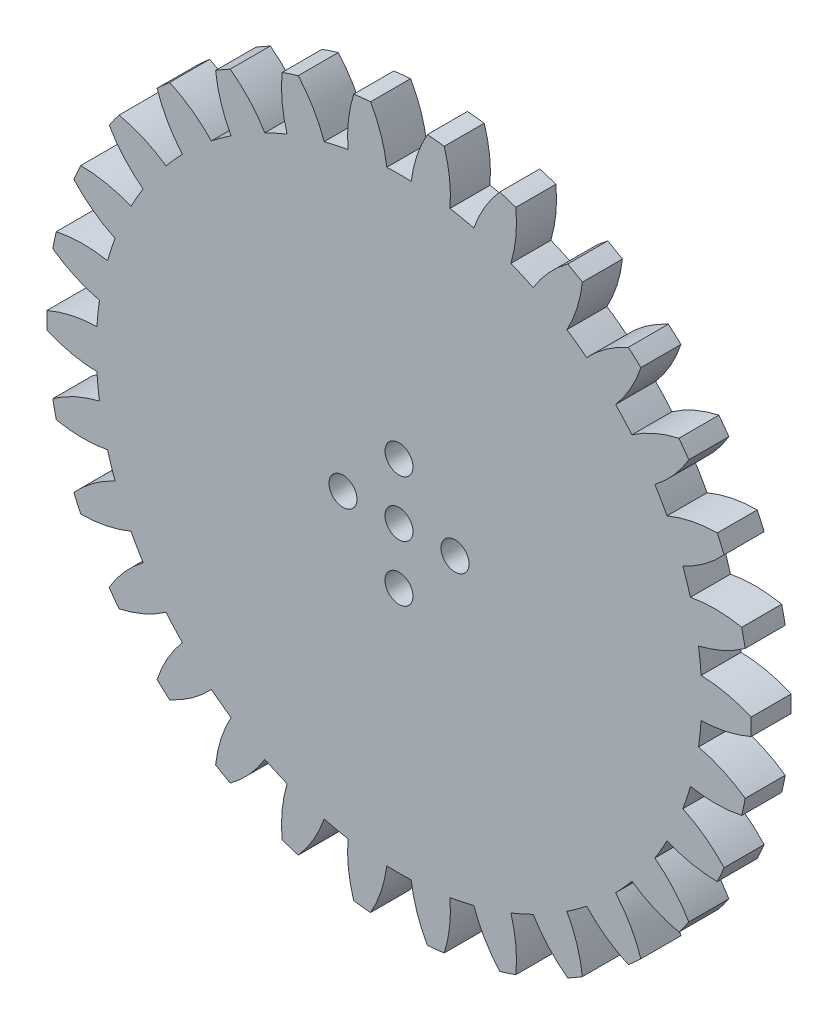
SolidWorks part; units mm, degrees
ref_plane "前视基准面" through (0, 0, 0) normal (0, 0, 1) x (1, 0, 0)
ref_plane "上视基准面" through (0, 0, 0) normal (0, 1, 0) x (1, 0, 0)
ref_plane "右视基准面" through (0, 0, 0) normal (1, 0, 0) x (0, 0, -1)
sketch "草图1" plane through (0, 0, 0) normal (0, 0, 1) x (1, 0, 0)
  arc A0 (-43.9873, -1.0569) -> (-37.7331, -2.4344) centre (-37.3786, 14.0618) ccw
  arc A1 (-37.7331, -2.4344) -> (-37.4146, -5.4639) centre (0, 0) ccw
  arc A2 (-37.4146, -5.4639) -> (-43.2458, -8.1117) centre (-33.6381, -21.5259) ccw
  arc A3 (-43.2458, -8.1117) -> (-42.8063, -10.1793) centre (0, 0) ccw
  arc A4 (-42.8063, -10.1793) -> (-36.4024, -10.2263) centre (-39.4854, 5.9831) ccw
  arc A5 (-36.4024, -10.2263) -> (-35.461, -13.1235) centre (0, 0) ccw
  arc A6 (-35.461, -13.1235) -> (-40.6143, -16.9257) centre (-28.4276, -28.0493) ccw
  arc A7 (-40.6143, -16.9257) -> (-39.7545, -18.8568) centre (0, 0) ccw
  arc A8 (-39.7545, -18.8568) -> (-33.4807, -17.5714) centre (-39.8665, -2.3572) ccw
  arc A9 (-33.4807, -17.5714) -> (-31.9576, -20.2095) centre (0, 0) ccw
  arc A10 (-31.9576, -20.2095) -> (-36.2077, -25) centre (-21.9746, -33.3468) ccw
  arc A11 (-36.2077, -25) -> (-34.9652, -26.7101) centre (0, 0) ccw
  arc A12 (-34.9652, -26.7101) -> (-29.0958, -24.1484) centre (-38.5052, -10.5943) ccw
  arc A13 (-29.0958, -24.1484) -> (-27.0575, -26.4122) centre (0, 0) ccw
  arc A14 (-27.0575, -26.4122) -> (-30.2187, -31.9817) centre (-14.5612, -37.1869) ccw
  arc A15 (-30.2187, -31.9817) -> (-28.6478, -33.3961) centre (0, 0) ccw
  arc A16 (-28.6478, -33.3961) -> (-23.4392, -29.6701) centre (-35.4611, -18.3685) ccw
  arc A17 (-23.4392, -29.6701) -> (-20.9748, -31.4606) centre (0, 0) ccw
  arc A18 (-20.9748, -31.4606) -> (-22.909, -37.5657) centre (-6.5114, -39.4017) ccw
  arc A19 (-22.909, -37.5657) -> (-21.0784, -38.6226) centre (0, 0) ccw
  arc A20 (-21.0784, -38.6226) -> (-16.7583, -33.895) centre (-30.8672, -25.3399) ccw
  arc A21 (-16.7583, -33.895) -> (-13.9754, -35.134) centre (0, 0) ccw
  arc A22 (-13.9754, -35.134) -> (-14.598, -41.5078) centre (1.8229, -39.8945) ccw
  arc A23 (-14.598, -41.5078) -> (-12.5877, -42.161) centre (0, 0) ccw
  arc A24 (-12.5877, -42.161) -> (-9.3449, -36.6385) centre (-24.9242, -31.2038) ccw
  arc A25 (-9.3449, -36.6385) -> (-6.3652, -37.2719) centre (0, 0) ccw
  arc A26 (-6.3652, -37.2719) -> (-5.649, -43.6359) centre (10.0776, -38.6437) ccw
  arc A27 (-5.649, -43.6359) -> (-3.5468, -43.8568) centre (0, 0) ccw
  arc A28 (-3.5468, -43.8568) -> (-1.5231, -37.7808) centre (-17.8919, -35.7039) ccw
  arc A29 (-1.5231, -37.7808) -> (1.5231, -37.7808) centre (0, 0) ccw
  arc A30 (1.5231, -37.7808) -> (3.5468, -43.8568) centre (17.8919, -35.7039) ccw
  arc A31 (3.5468, -43.8568) -> (5.649, -43.6359) centre (0, 0) ccw
  arc A32 (5.649, -43.6359) -> (6.3652, -37.2719) centre (-10.0776, -38.6437) ccw
  arc A33 (6.3652, -37.2719) -> (9.3449, -36.6385) centre (0, 0) ccw
  arc A34 (9.3449, -36.6385) -> (12.5877, -42.161) centre (24.9242, -31.2038) ccw
  arc A35 (12.5877, -42.161) -> (14.598, -41.5078) centre (0, 0) ccw
  arc A36 (14.598, -41.5078) -> (13.9754, -35.134) centre (-1.8229, -39.8945) ccw
  arc A37 (13.9754, -35.134) -> (16.7583, -33.895) centre (0, 0) ccw
  arc A38 (16.7583, -33.895) -> (21.0784, -38.6226) centre (30.8672, -25.3399) ccw
  arc A39 (21.0784, -38.6226) -> (22.909, -37.5657) centre (0, 0) ccw
  arc A40 (22.909, -37.5657) -> (20.9748, -31.4606) centre (6.5114, -39.4017) ccw
  arc A41 (20.9748, -31.4606) -> (23.4392, -29.6701) centre (0, 0) ccw
  arc A42 (23.4392, -29.6701) -> (28.6478, -33.3961) centre (35.4611, -18.3685) ccw
  arc A43 (28.6478, -33.3961) -> (30.2187, -31.9817) centre (0, 0) ccw
  arc A44 (30.2187, -31.9817) -> (27.0575, -26.4122) centre (14.5612, -37.1869) ccw
  arc A45 (27.0575, -26.4122) -> (29.0958, -24.1484) centre (0, 0) ccw
  arc A46 (29.0958, -24.1484) -> (34.9652, -26.7101) centre (38.5052, -10.5943) ccw
  arc A47 (34.9652, -26.7101) -> (36.2077, -25) centre (0, 0) ccw
  arc A48 (36.2077, -25) -> (31.9576, -20.2095) centre (21.9746, -33.3468) ccw
  arc A49 (31.9576, -20.2095) -> (33.4807, -17.5714) centre (0, 0) ccw
  arc A50 (33.4807, -17.5714) -> (39.7545, -18.8568) centre (39.8665, -2.3572) ccw
  arc A51 (39.7545, -18.8568) -> (40.6143, -16.9257) centre (0, 0) ccw
  arc A52 (40.6143, -16.9257) -> (35.461, -13.1235) centre (28.4276, -28.0493) ccw
  arc A53 (35.461, -13.1235) -> (36.4024, -10.2263) centre (0, 0) ccw
  arc A54 (36.4024, -10.2263) -> (42.8063, -10.1793) centre (39.4854, 5.9831) ccw
  arc A55 (42.8063, -10.1793) -> (43.2458, -8.1117) centre (0, 0) ccw
  arc A56 (43.2458, -8.1117) -> (37.4146, -5.4639) centre (33.6381, -21.5259) ccw
  arc A57 (37.4146, -5.4639) -> (37.7331, -2.4344) centre (0, 0) ccw
  arc A58 (37.7331, -2.4344) -> (43.9873, -1.0569) centre (37.3786, 14.0618) ccw
  arc A59 (43.9873, -1.0569) -> (43.9873, 1.0569) centre (0, 0) ccw
  arc A60 (43.9873, 1.0569) -> (37.7331, 2.4344) centre (37.3786, -14.0618) ccw
  arc A61 (37.7331, 2.4344) -> (37.4146, 5.4639) centre (0, 0) ccw
  arc A62 (37.4146, 5.4639) -> (43.2458, 8.1117) centre (33.6381, 21.5259) ccw
  arc A63 (43.2458, 8.1117) -> (42.8063, 10.1793) centre (0, 0) ccw
  arc A64 (42.8063, 10.1793) -> (36.4024, 10.2263) centre (39.4854, -5.9831) ccw
  arc A65 (36.4024, 10.2263) -> (35.461, 13.1235) centre (0, 0) ccw
  arc A66 (35.461, 13.1235) -> (40.6143, 16.9257) centre (28.4276, 28.0493) ccw
  arc A67 (40.6143, 16.9257) -> (39.7545, 18.8568) centre (0, 0) ccw
  arc A68 (39.7545, 18.8568) -> (33.4807, 17.5714) centre (39.8665, 2.3572) ccw
  arc A69 (33.4807, 17.5714) -> (31.9576, 20.2095) centre (0, 0) ccw
  arc A70 (31.9576, 20.2095) -> (36.2077, 25) centre (21.9746, 33.3468) ccw
  arc A71 (36.2077, 25) -> (34.9652, 26.7101) centre (0, 0) ccw
  arc A72 (34.9652, 26.7101) -> (29.0958, 24.1484) centre (38.5052, 10.5943) ccw
  arc A73 (29.0958, 24.1484) -> (27.0575, 26.4122) centre (0, 0) ccw
  arc A74 (27.0575, 26.4122) -> (30.2187, 31.9817) centre (14.5612, 37.1869) ccw
  arc A75 (30.2187, 31.9817) -> (28.6478, 33.3961) centre (0, 0) ccw
  arc A76 (28.6478, 33.3961) -> (23.4392, 29.6701) centre (35.4611, 18.3685) ccw
  arc A77 (23.4392, 29.6701) -> (20.9748, 31.4606) centre (0, 0) ccw
  arc A78 (20.9748, 31.4606) -> (22.909, 37.5657) centre (6.5114, 39.4017) ccw
  arc A79 (22.909, 37.5657) -> (21.0784, 38.6226) centre (0, 0) ccw
  arc A80 (21.0784, 38.6226) -> (16.7583, 33.895) centre (30.8672, 25.3399) ccw
  arc A81 (16.7583, 33.895) -> (13.9754, 35.134) centre (0, 0) ccw
  arc A82 (13.9754, 35.134) -> (14.598, 41.5078) centre (-1.8229, 39.8945) ccw
  arc A83 (14.598, 41.5078) -> (12.5877, 42.161) centre (0, 0) ccw
  arc A84 (12.5877, 42.161) -> (9.3449, 36.6385) centre (24.9242, 31.2038) ccw
  arc A85 (9.3449, 36.6385) -> (6.3652, 37.2719) centre (0, 0) ccw
  arc A86 (6.3652, 37.2719) -> (5.649, 43.6359) centre (-10.0776, 38.6437) ccw
  arc A87 (5.649, 43.6359) -> (3.5468, 43.8568) centre (0, 0) ccw
  arc A88 (3.5468, 43.8568) -> (1.5231, 37.7808) centre (17.8919, 35.7039) ccw
  arc A89 (1.5231, 37.7808) -> (-1.5231, 37.7808) centre (0, 0) ccw
  arc A90 (-1.5231, 37.7808) -> (-3.5468, 43.8568) centre (-17.8919, 35.7039) ccw
  arc A91 (-3.5468, 43.8568) -> (-5.649, 43.6359) centre (0, 0) ccw
  arc A92 (-5.649, 43.6359) -> (-6.3652, 37.2719) centre (10.0776, 38.6437) ccw
  arc A93 (-6.3652, 37.2719) -> (-9.3449, 36.6385) centre (0, 0) ccw
  arc A94 (-9.3449, 36.6385) -> (-12.5877, 42.161) centre (-24.9242, 31.2038) ccw
  arc A95 (-12.5877, 42.161) -> (-14.598, 41.5078) centre (0, 0) ccw
  arc A96 (-14.598, 41.5078) -> (-13.9754, 35.134) centre (1.8229, 39.8945) ccw
  arc A97 (-13.9754, 35.134) -> (-16.7583, 33.895) centre (0, 0) ccw
  arc A98 (-16.7583, 33.895) -> (-21.0784, 38.6226) centre (-30.8672, 25.3399) ccw
  arc A99 (-21.0784, 38.6226) -> (-22.909, 37.5657) centre (0, 0) ccw
  arc A100 (-22.909, 37.5657) -> (-20.9748, 31.4606) centre (-6.5114, 39.4017) ccw
  arc A101 (-20.9748, 31.4606) -> (-23.4392, 29.6701) centre (0, 0) ccw
  arc A102 (-23.4392, 29.6701) -> (-28.6478, 33.3961) centre (-35.4611, 18.3685) ccw
  arc A103 (-28.6478, 33.3961) -> (-30.2187, 31.9817) centre (0, 0) ccw
  arc A104 (-30.2187, 31.9817) -> (-27.0575, 26.4122) centre (-14.5612, 37.1869) ccw
  arc A105 (-27.0575, 26.4122) -> (-29.0958, 24.1484) centre (0, 0) ccw
  arc A106 (-29.0958, 24.1484) -> (-34.9652, 26.7101) centre (-38.5052, 10.5943) ccw
  arc A107 (-34.9652, 26.7101) -> (-36.2077, 25) centre (0, 0) ccw
  arc A108 (-36.2077, 25) -> (-31.9576, 20.2095) centre (-21.9746, 33.3468) ccw
  arc A109 (-31.9576, 20.2095) -> (-33.4807, 17.5714) centre (0, 0) ccw
  arc A110 (-33.4807, 17.5714) -> (-39.7545, 18.8568) centre (-39.8665, 2.3572) ccw
  arc A111 (-39.7545, 18.8568) -> (-40.6143, 16.9257) centre (0, 0) ccw
  arc A112 (-40.6143, 16.9257) -> (-35.461, 13.1235) centre (-28.4276, 28.0493) ccw
  arc A113 (-35.461, 13.1235) -> (-36.4024, 10.2263) centre (0, 0) ccw
  arc A114 (-36.4024, 10.2263) -> (-42.8063, 10.1793) centre (-39.4854, -5.9831) ccw
  arc A115 (-42.8063, 10.1793) -> (-43.2458, 8.1117) centre (0, 0) ccw
  arc A116 (-43.2458, 8.1117) -> (-37.4146, 5.4639) centre (-33.6381, 21.5259) ccw
  arc A117 (-37.4146, 5.4639) -> (-37.7331, 2.4344) centre (0, 0) ccw
  arc A118 (-37.7331, 2.4344) -> (-43.9873, 1.0569) centre (-37.3786, -14.0618) ccw
  arc A119 (-43.9873, 1.0569) -> (-43.9873, -1.0569) centre (0, 0) ccw
  circle A120 centre (0, 0) radius 7 construction
  circle A121 centre (0, 7) radius 1.75
  circle A122 centre (7, 0) radius 1.75
  circle A123 centre (0, -7) radius 1.75
  circle A124 centre (-7, 0) radius 1.75
  circle A125 centre (0, 0) radius 1.75
  point P252 (0, 0)
  dimension "D1" = 37.8115
  dimension "D2" = 14
  dimension "D3" = 3.5
  dimension "D5" = 3.5
  dimension "D4" = 4
extrude "凸台-拉伸1" add sketch "草图1" along normal blind 5
scale "缩放比例1" scale about centroid uniform scaling yes scale factor 0.95
